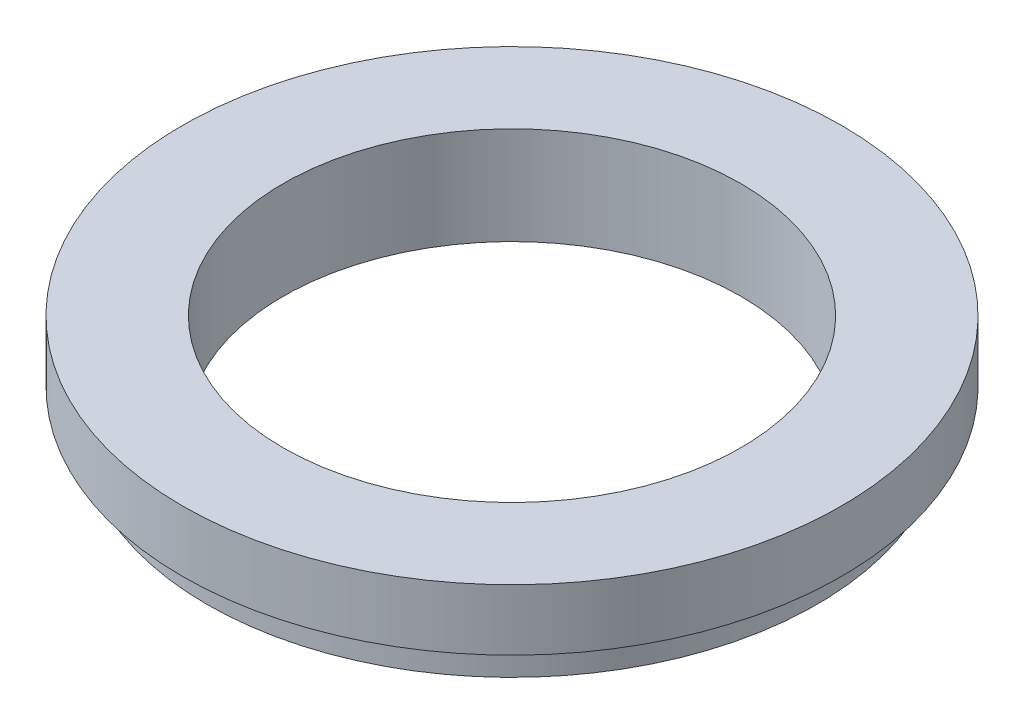
SolidWorks part; units mm, degrees
ref_plane "Front Plane" through (0, 0, 0) normal (0, 0, 1) x (1, 0, 0)
ref_plane "Top Plane" through (0, 0, 0) normal (0, 1, 0) x (1, 0, 0)
ref_plane "Right Plane" through (0, 0, 0) normal (1, 0, 0) x (0, 0, -1)
sketch "Sketch1" plane through (0, 0, 0) normal (0, 0, 1) x (1, 0, 0)
  line L0 (6.3462, 0) -> (6.3462, 0.762)
  line L1 (6.3462, 0.762) -> (6.858, 0.762)
  line L2 (6.858, 0.762) -> (6.858, 2.032)
  line L3 (6.858, 2.032) -> (4.7625, 2.032)
  line L4 (4.7625, 2.032) -> (4.7625, 0)
  line L5 (4.7625, 0) -> (6.3462, 0)
  line L6 (0, 2.032) -> (0, 0) construction
revolve "Revolve1" add sketch "Sketch1" angle 360 about L6
